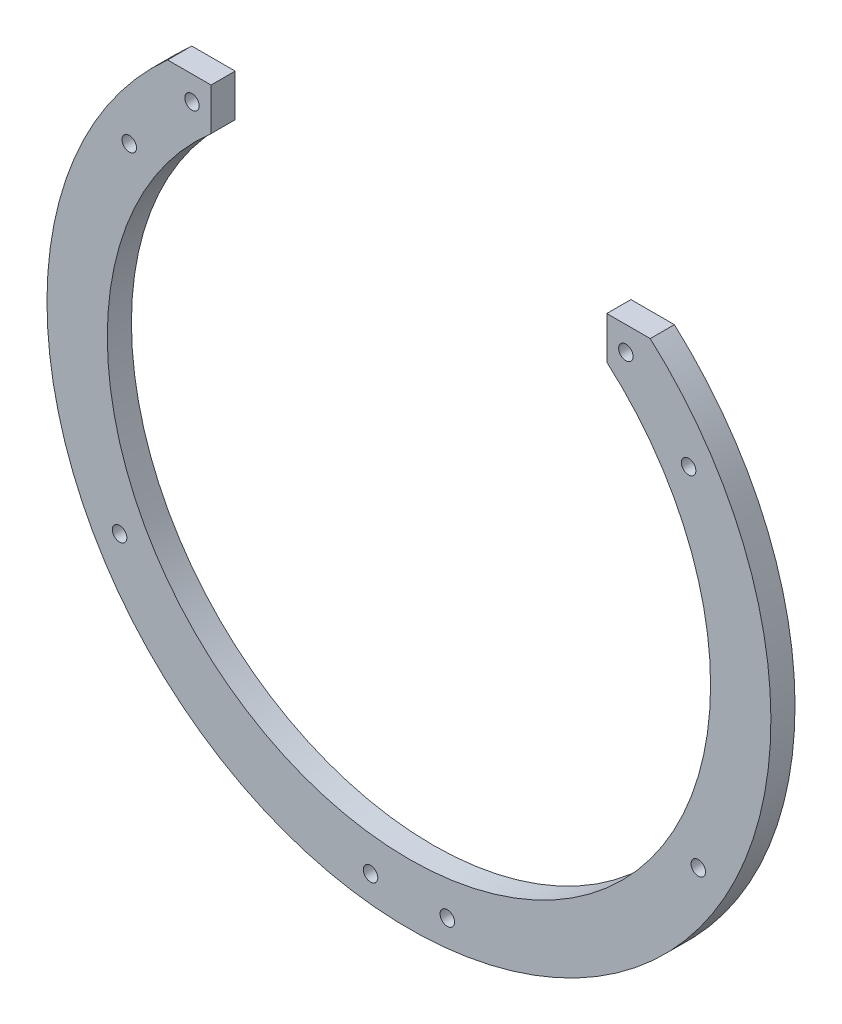
SolidWorks part; units mm, degrees
material "Acrílico (médio-alto impacto)"
ref_plane "Plano frontal" through (0, 0, 0) normal (0, 0, 1) x (1, 0, 0)
ref_plane "Plano superior" through (0, 0, 0) normal (0, 1, 0) x (1, 0, 0)
ref_plane "Plano direito" through (0, 0, 0) normal (1, 0, 0) x (0, 0, -1)
sketch "Esboço1" plane through (0, 0, 0) normal (0, 0, 1) x (1, 0, 0)
  line L0 (44.4954, -168.4305) -> (22.4463, -168.4305)
  line L1 (-33.4554, -168.4305) -> (-55.5046, -168.4305) construction
  line L10 (-55.5046, -168.4305) -> (-55.5734, -168.3931)
  arc A0 (-55.5046, -168.4305) -> (44.4954, -168.4305) centre (-5.5046, -224.3322) ccw
  arc A1 (-33.4554, -168.4305) -> (22.4463, -168.4305) centre (-5.5046, -224.3322) ccw
  dimension "D1" = 150
  dimension "D2" = 125
extrude "Ressalto-extrusão1" add sketch "Esboço1" along normal blind 5 contours A1 L1 A0 L0
sketch "Esboço2" plane through (0, 0, 5) normal (0, 0, 1) x (1, 0, 0)
  line L1 (-5.5046, -299.3322) -> (-5.5046, -271.3491) construction
  circle A0 centre (39.4463, -173.4305) radius 1.5
  circle A1 centre (52.4463, -187.4305) radius 1.5
  circle A2 centre (54.4463, -258.4305) radius 1.5
  circle A3 centre (-13.4554, -293.4305) radius 1.5
  circle A4 centre (2.4463, -293.4305) radius 1.5
  circle A5 centre (-65.4554, -258.4305) radius 1.5
  circle A8 centre (-63.4554, -187.4305) radius 1.5
  circle A9 centre (-50.4554, -173.4305) radius 1.5
  dimension "D3" = 3
  dimension "D6" = 3
  dimension "D9" = 3
  dimension "D12" = 3
extrude "Corte-extrusão1" cut sketch "Esboço2" against normal through all
sketch "Esboço3" plane through (0, 0, 5) normal (0, 0, 1) x (1, 0, 0)
  line L1 (35.4954, -179.9414) -> (-46.5046, -179.9414)
  line L2 (35.4954, -179.9414) -> (35.4954, -161.1485)
  line L3 (35.4954, -161.1485) -> (-46.5046, -161.1485)
  line L4 (-46.5046, -179.9414) -> (-46.5046, -161.1485)
  dimension "D1" = 9
  dimension "D2" = 9
extrude "Corte-extrusão2" cut sketch "Esboço3" against normal blind 10
